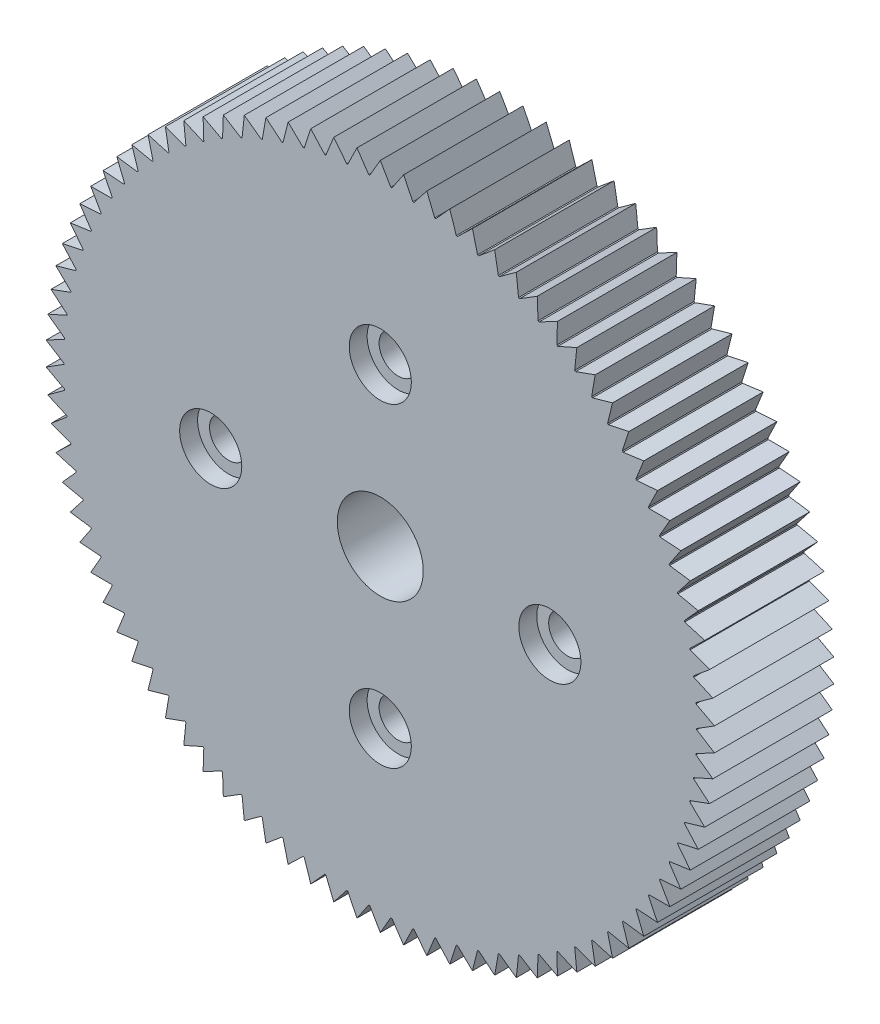
SolidWorks part; units mm, degrees
ref_plane "Front Plane" through (0, 0, 0) normal (0, 0, 1) x (1, 0, 0)
ref_plane "Top Plane" through (0, 0, 0) normal (0, 1, 0) x (1, 0, 0)
ref_plane "Right Plane" through (0, 0, 0) normal (1, 0, 0) x (0, 0, -1)
sketch "Sketch1" plane through (0, 0, 0) normal (0, 0, 1) x (1, 0, 0)
  circle A0 centre (0, 0) radius 13.25
  dimension "D1" = 26.5
extrude "Extrude1" add sketch "Sketch1" along normal blind 5
sketch "Sketch2" plane through (0, 0, 0) normal (0, 0, -1) x (-1, 0, 0)
  line L0 (-7.1, 1.675) -> (-2.3674, 1.675)
  line L1 (1.675, 6.6) -> (1.675, 2.3674)
  line L2 (-7.1, -1.675) -> (-2.3674, -1.675)
  line L3 (-1.675, 6.6) -> (-1.675, 2.3674)
  line L4 (-1.675, -2.3674) -> (-1.675, -6.6)
  line L5 (1.675, -2.3674) -> (1.675, -6.6)
  line L6 (2.3674, -1.675) -> (7.1, -1.675)
  line L7 (2.3674, 1.675) -> (7.1, 1.675)
  circle A0 centre (0, -6.6) radius 1.675 construction
  circle A1 centre (0, 6.6) radius 1.675 construction
  circle A2 centre (-7.1, 0) radius 1.675 construction
  circle A3 centre (7.1, 0) radius 1.675 construction
  arc A4 (-2.3674, -1.675) -> (-1.675, -2.3674) centre (0, 0) ccw
  arc A5 (-7.1, 1.675) -> (-7.1, -1.675) centre (-7.1, 0) ccw
  arc A6 (-1.675, -6.6) -> (1.675, -6.6) centre (0, -6.6) ccw
  arc A7 (7.1, 1.675) -> (7.1, -1.675) centre (7.1, 0) cw
  arc A8 (-1.675, 6.6) -> (1.675, 6.6) centre (0, 6.6) cw
  circle A9 centre (0, 0) radius 2.9 construction
  arc A10 (-2.3674, 1.675) -> (-1.675, 2.3674) centre (0, 0) cw
  arc A11 (1.675, 2.3674) -> (2.3674, 1.675) centre (0, 0) cw
  arc A12 (2.3674, -1.675) -> (1.675, -2.3674) centre (0, 0) cw
  dimension "D1" = 4.7326
extrude "Extrude2" cut sketch "Sketch2" against normal blind 1.2
sketch "Sketch3" plane through (0, 0, 1.2) normal (0, 0, -1) x (-1, 0, 0)
  circle A0 centre (0, 0) radius 1.8
extrude "Extrude3" cut sketch "Sketch3" against normal through all
sketch "Sketch4" plane through (0, 0, 1.2) normal (0, 0, -1) x (-1, 0, 0)
  circle A0 centre (0, 6.6) radius 0.8
  circle A1 centre (-7.1, 0) radius 0.8
  circle A2 centre (0, -6.6) radius 0.8
  circle A3 centre (7.1, 0) radius 0.8
extrude "Extrude4" cut sketch "Sketch4" against normal through all
sketch "Sketch5" plane through (0, 0, 5) normal (0, 0, 1) x (1, 0, 0)
  circle A0 centre (-7.1, 0) radius 1.3
  circle A1 centre (0, -6.6) radius 1.3
  circle A2 centre (7.1, 0) radius 1.3
  circle A3 centre (0, 6.6) radius 1.3
extrude "Extrude5" cut sketch "Sketch5" against normal blind 0.75
sketch "Sketch6" plane through (0, 0, 0) normal (0, 0, -1) x (-1, 0, 0)
  line L0 (0, 13.25) -> (0, 14) construction
  line L1 (0, 14) -> (-0.4393, 13.2427)
  line L2 (0.4393, 13.2427) -> (0, 14)
  line L181 (1.362, 13.1798) -> (0.9766, 13.9659)
  line L182 (0.9766, 13.9659) -> (0.4855, 13.2411)
  line L183 (2.2781, 13.0527) -> (1.9484, 13.8638)
  line L184 (1.9484, 13.8638) -> (1.408, 13.175)
  line L185 (3.183, 12.862) -> (2.9108, 13.6941)
  line L186 (2.9108, 13.6941) -> (2.3236, 13.0447)
  line L187 (4.0725, 12.6086) -> (3.8589, 13.4577)
  line L188 (3.8589, 13.4577) -> (3.2279, 12.8508)
  line L189 (4.9421, 12.2938) -> (4.7883, 13.1557)
  line L190 (4.7883, 13.1557) -> (4.1165, 12.5943)
  line L191 (5.7876, 11.9191) -> (5.6943, 12.7896)
  line L192 (5.6943, 12.7896) -> (4.985, 12.2765)
  line L193 (6.605, 11.4864) -> (6.5726, 12.3613)
  line L194 (6.5726, 12.3613) -> (5.8292, 11.8989)
  line L195 (7.3901, 10.9977) -> (7.4189, 11.8727)
  line L196 (7.4189, 11.8727) -> (6.645, 11.4633)
  line L197 (8.1393, 10.4554) -> (8.229, 11.3262)
  line L198 (8.229, 11.3262) -> (7.4285, 10.9718)
  line L199 (8.8488, 9.8621) -> (8.999, 10.7246)
  line L200 (8.999, 10.7246) -> (8.1757, 10.4269)
  line L201 (9.5152, 9.2208) -> (9.7252, 10.0708)
  line L202 (9.7252, 10.0708) -> (8.8832, 9.8312)
  line L203 (10.1352, 8.5346) -> (10.404, 9.3678)
  line L204 (10.404, 9.3678) -> (9.5473, 9.1876)
  line L205 (10.7059, 7.8069) -> (11.0322, 8.6193)
  line L206 (11.0322, 8.6193) -> (10.1649, 8.4992)
  line L207 (11.2244, 7.041) -> (11.6065, 7.8287)
  line L208 (11.6065, 7.8287) -> (10.7331, 7.7694)
  line L209 (11.6882, 6.2409) -> (12.1244, 7)
  line L210 (12.1244, 7) -> (11.2489, 7.0018)
  line L211 (12.0951, 5.4104) -> (12.5831, 6.1372)
  line L212 (12.5831, 6.1372) -> (11.7099, 6.2001)
  line L213 (12.443, 4.5535) -> (12.9806, 5.2445)
  line L214 (12.9806, 5.2445) -> (12.1139, 5.3681)
  line L215 (12.7303, 3.6744) -> (13.3148, 4.3262)
  line L216 (13.3148, 4.3262) -> (12.4588, 4.51)
  line L217 (12.9556, 2.7774) -> (13.5841, 3.3869)
  line L218 (13.5841, 3.3869) -> (12.7431, 3.63)
  line L219 (13.1178, 1.8669) -> (13.7873, 2.4311)
  line L220 (13.7873, 2.4311) -> (12.9652, 2.7322)
  line L221 (13.2161, 0.9473) -> (13.9233, 1.4634)
  line L222 (13.9233, 1.4634) -> (13.1243, 1.8211)
  line L223 (13.25, 0.0231) -> (13.9915, 0.4886)
  line L224 (13.9915, 0.4886) -> (13.2193, 0.9012)
  line L225 (13.2193, -0.9012) -> (13.9915, -0.4886)
  line L226 (13.9915, -0.4886) -> (13.25, -0.0231)
  line L227 (13.1243, -1.8211) -> (13.9233, -1.4634)
  line L228 (13.9233, -1.4634) -> (13.2161, -0.9473)
  line L229 (12.9652, -2.7322) -> (13.7873, -2.4311)
  line L230 (13.7873, -2.4311) -> (13.1178, -1.8669)
  line L231 (12.7431, -3.63) -> (13.5841, -3.3869)
  line L232 (13.5841, -3.3869) -> (12.9556, -2.7774)
  line L233 (12.4588, -4.51) -> (13.3148, -4.3262)
  line L234 (13.3148, -4.3262) -> (12.7303, -3.6744)
  line L235 (12.1139, -5.3681) -> (12.9806, -5.2445)
  line L236 (12.9806, -5.2445) -> (12.443, -4.5535)
  line L237 (11.7099, -6.2001) -> (12.5831, -6.1372)
  line L238 (12.5831, -6.1372) -> (12.0951, -5.4104)
  line L239 (11.2489, -7.0018) -> (12.1244, -7)
  line L240 (12.1244, -7) -> (11.6882, -6.2409)
  line L241 (10.7331, -7.7694) -> (11.6065, -7.8287)
  line L242 (11.6065, -7.8287) -> (11.2244, -7.041)
  line L243 (10.1649, -8.4992) -> (11.0322, -8.6193)
  line L244 (11.0322, -8.6193) -> (10.7059, -7.8069)
  line L245 (9.5473, -9.1876) -> (10.404, -9.3678)
  line L246 (10.404, -9.3678) -> (10.1352, -8.5346)
  line L247 (8.8832, -9.8312) -> (9.7252, -10.0708)
  line L248 (9.7252, -10.0708) -> (9.5152, -9.2208)
  line L249 (8.1757, -10.4269) -> (8.999, -10.7246)
  line L250 (8.999, -10.7246) -> (8.8488, -9.8621)
  line L251 (7.4285, -10.9718) -> (8.229, -11.3262)
  line L252 (8.229, -11.3262) -> (8.1393, -10.4554)
  line L253 (6.645, -11.4633) -> (7.4189, -11.8727)
  line L254 (7.4189, -11.8727) -> (7.3901, -10.9977)
  line L255 (5.8292, -11.8989) -> (6.5726, -12.3613)
  line L256 (6.5726, -12.3613) -> (6.605, -11.4864)
  line L257 (4.985, -12.2765) -> (5.6943, -12.7896)
  line L258 (5.6943, -12.7896) -> (5.7876, -11.9191)
  line L259 (4.1165, -12.5943) -> (4.7883, -13.1557)
  line L260 (4.7883, -13.1557) -> (4.9421, -12.2938)
  line L261 (3.2279, -12.8508) -> (3.8589, -13.4577)
  line L262 (3.8589, -13.4577) -> (4.0725, -12.6086)
  line L263 (2.3236, -13.0447) -> (2.9108, -13.6941)
  line L264 (2.9108, -13.6941) -> (3.183, -12.862)
  line L265 (1.408, -13.175) -> (1.9484, -13.8638)
  line L266 (1.9484, -13.8638) -> (2.2781, -13.0527)
  line L267 (0.4855, -13.2411) -> (0.9766, -13.9659)
  line L268 (0.9766, -13.9659) -> (1.362, -13.1798)
  line L269 (-0.4393, -13.2427) -> (0, -14)
  line L270 (0, -14) -> (0.4393, -13.2427)
  line L271 (-1.362, -13.1798) -> (-0.9766, -13.9659)
  line L272 (-0.9766, -13.9659) -> (-0.4855, -13.2411)
  line L273 (-2.2781, -13.0527) -> (-1.9484, -13.8638)
  line L274 (-1.9484, -13.8638) -> (-1.408, -13.175)
  line L275 (-3.183, -12.862) -> (-2.9108, -13.6941)
  line L276 (-2.9108, -13.6941) -> (-2.3236, -13.0447)
  line L277 (-4.0725, -12.6086) -> (-3.8589, -13.4577)
  line L278 (-3.8589, -13.4577) -> (-3.2279, -12.8508)
  line L279 (-4.9421, -12.2938) -> (-4.7883, -13.1557)
  line L280 (-4.7883, -13.1557) -> (-4.1165, -12.5943)
  line L281 (-5.7876, -11.9191) -> (-5.6943, -12.7896)
  line L282 (-5.6943, -12.7896) -> (-4.985, -12.2765)
  line L283 (-6.605, -11.4864) -> (-6.5726, -12.3613)
  line L284 (-6.5726, -12.3613) -> (-5.8292, -11.8989)
  line L285 (-7.3901, -10.9977) -> (-7.4189, -11.8727)
  line L286 (-7.4189, -11.8727) -> (-6.645, -11.4633)
  line L287 (-8.1393, -10.4554) -> (-8.229, -11.3262)
  line L288 (-8.229, -11.3262) -> (-7.4285, -10.9718)
  line L289 (-8.8488, -9.8621) -> (-8.999, -10.7246)
  line L290 (-8.999, -10.7246) -> (-8.1757, -10.4269)
  line L291 (-9.5152, -9.2208) -> (-9.7252, -10.0708)
  line L292 (-9.7252, -10.0708) -> (-8.8832, -9.8312)
  line L293 (-10.1352, -8.5346) -> (-10.404, -9.3678)
  line L294 (-10.404, -9.3678) -> (-9.5473, -9.1876)
  line L295 (-10.7059, -7.8069) -> (-11.0322, -8.6193)
  line L296 (-11.0322, -8.6193) -> (-10.1649, -8.4992)
  line L297 (-11.2244, -7.041) -> (-11.6065, -7.8287)
  line L298 (-11.6065, -7.8287) -> (-10.7331, -7.7694)
  line L299 (-11.6882, -6.2409) -> (-12.1244, -7)
  line L300 (-12.1244, -7) -> (-11.2489, -7.0018)
  line L301 (-12.0951, -5.4104) -> (-12.5831, -6.1372)
  line L302 (-12.5831, -6.1372) -> (-11.7099, -6.2001)
  line L303 (-12.443, -4.5535) -> (-12.9806, -5.2445)
  line L304 (-12.9806, -5.2445) -> (-12.1139, -5.3681)
  line L305 (-12.7303, -3.6744) -> (-13.3148, -4.3262)
  line L306 (-13.3148, -4.3262) -> (-12.4588, -4.51)
  line L307 (-12.9556, -2.7774) -> (-13.5841, -3.3869)
  line L308 (-13.5841, -3.3869) -> (-12.7431, -3.63)
  line L309 (-13.1178, -1.8669) -> (-13.7873, -2.4311)
  line L310 (-13.7873, -2.4311) -> (-12.9652, -2.7322)
  line L311 (-13.2161, -0.9473) -> (-13.9233, -1.4634)
  line L312 (-13.9233, -1.4634) -> (-13.1243, -1.8211)
  line L313 (-13.25, -0.0231) -> (-13.9915, -0.4886)
  line L314 (-13.9915, -0.4886) -> (-13.2193, -0.9012)
  line L315 (-13.2193, 0.9012) -> (-13.9915, 0.4886)
  line L316 (-13.9915, 0.4886) -> (-13.25, 0.0231)
  line L317 (-13.1243, 1.8211) -> (-13.9233, 1.4634)
  line L318 (-13.9233, 1.4634) -> (-13.2161, 0.9473)
  line L319 (-12.9652, 2.7322) -> (-13.7873, 2.4311)
  line L320 (-13.7873, 2.4311) -> (-13.1178, 1.8669)
  line L321 (-12.7431, 3.63) -> (-13.5841, 3.3869)
  line L322 (-13.5841, 3.3869) -> (-12.9556, 2.7774)
  line L323 (-12.4588, 4.51) -> (-13.3148, 4.3262)
  line L324 (-13.3148, 4.3262) -> (-12.7303, 3.6744)
  line L325 (-12.1139, 5.3681) -> (-12.9806, 5.2445)
  line L326 (-12.9806, 5.2445) -> (-12.443, 4.5535)
  line L327 (-11.7099, 6.2001) -> (-12.5831, 6.1372)
  line L328 (-12.5831, 6.1372) -> (-12.0951, 5.4104)
  line L329 (-11.2489, 7.0018) -> (-12.1244, 7)
  line L330 (-12.1244, 7) -> (-11.6882, 6.2409)
  line L331 (-10.7331, 7.7694) -> (-11.6065, 7.8287)
  line L332 (-11.6065, 7.8287) -> (-11.2244, 7.041)
  line L333 (-10.1649, 8.4992) -> (-11.0322, 8.6193)
  line L334 (-11.0322, 8.6193) -> (-10.7059, 7.8069)
  line L335 (-9.5473, 9.1876) -> (-10.404, 9.3678)
  line L336 (-10.404, 9.3678) -> (-10.1352, 8.5346)
  line L337 (-8.8832, 9.8312) -> (-9.7252, 10.0708)
  line L338 (-9.7252, 10.0708) -> (-9.5152, 9.2208)
  line L339 (-8.1757, 10.4269) -> (-8.999, 10.7246)
  line L340 (-8.999, 10.7246) -> (-8.8488, 9.8621)
  line L341 (-7.4285, 10.9718) -> (-8.229, 11.3262)
  line L342 (-8.229, 11.3262) -> (-8.1393, 10.4554)
  line L343 (-6.645, 11.4633) -> (-7.4189, 11.8727)
  line L344 (-7.4189, 11.8727) -> (-7.3901, 10.9977)
  line L345 (-5.8292, 11.8989) -> (-6.5726, 12.3613)
  line L346 (-6.5726, 12.3613) -> (-6.605, 11.4864)
  line L347 (-4.985, 12.2765) -> (-5.6943, 12.7896)
  line L348 (-5.6943, 12.7896) -> (-5.7876, 11.9191)
  line L349 (-4.1165, 12.5943) -> (-4.7883, 13.1557)
  line L350 (-4.7883, 13.1557) -> (-4.9421, 12.2938)
  line L351 (-3.2279, 12.8508) -> (-3.8589, 13.4577)
  line L352 (-3.8589, 13.4577) -> (-4.0725, 12.6086)
  line L353 (-2.3236, 13.0447) -> (-2.9108, 13.6941)
  line L354 (-2.9108, 13.6941) -> (-3.183, 12.862)
  line L355 (-1.408, 13.175) -> (-1.9484, 13.8638)
  line L356 (-1.9484, 13.8638) -> (-2.2781, 13.0527)
  line L357 (-0.4855, 13.2411) -> (-0.9766, 13.9659)
  line L358 (-0.9766, 13.9659) -> (-1.362, 13.1798)
  circle A0 centre (0, 0) radius 13.25 construction
  arc A1 (-0.4393, 13.2427) -> (0.4393, 13.2427) centre (0, 0) cw
  arc A91 (0.4855, 13.2411) -> (1.362, 13.1798) centre (0, 0) cw
  arc A92 (1.408, 13.175) -> (2.2781, 13.0527) centre (0, 0) cw
  arc A93 (2.3236, 13.0447) -> (3.183, 12.862) centre (0, 0) cw
  arc A94 (3.2279, 12.8508) -> (4.0725, 12.6086) centre (0, 0) cw
  arc A95 (4.1165, 12.5943) -> (4.9421, 12.2938) centre (0, 0) cw
  arc A96 (4.985, 12.2765) -> (5.7876, 11.9191) centre (0, 0) cw
  arc A97 (5.8292, 11.8989) -> (6.605, 11.4864) centre (0, 0) cw
  arc A98 (6.645, 11.4633) -> (7.3901, 10.9977) centre (0, 0) cw
  arc A99 (7.4285, 10.9718) -> (8.1393, 10.4554) centre (0, 0) cw
  arc A100 (8.1757, 10.4269) -> (8.8488, 9.8621) centre (0, 0) cw
  arc A101 (8.8832, 9.8312) -> (9.5152, 9.2208) centre (0, 0) cw
  arc A102 (9.5473, 9.1876) -> (10.1352, 8.5346) centre (0, 0) cw
  arc A103 (10.1649, 8.4992) -> (10.7059, 7.8069) centre (0, 0) cw
  arc A104 (10.7331, 7.7694) -> (11.2244, 7.041) centre (0, 0) cw
  arc A105 (11.2489, 7.0018) -> (11.6882, 6.2409) centre (0, 0) cw
  arc A106 (11.7099, 6.2001) -> (12.0951, 5.4104) centre (0, 0) cw
  arc A107 (12.1139, 5.3681) -> (12.443, 4.5535) centre (0, 0) cw
  arc A108 (12.4588, 4.51) -> (12.7303, 3.6744) centre (0, 0) cw
  arc A109 (12.7431, 3.63) -> (12.9556, 2.7774) centre (0, 0) cw
  arc A110 (12.9652, 2.7322) -> (13.1178, 1.8669) centre (0, 0) cw
  arc A111 (13.1243, 1.8211) -> (13.2161, 0.9473) centre (0, 0) cw
  arc A112 (13.2193, 0.9012) -> (13.25, 0.0231) centre (0, 0) cw
  arc A113 (13.25, -0.0231) -> (13.2193, -0.9012) centre (0, 0) cw
  arc A114 (13.2161, -0.9473) -> (13.1243, -1.8211) centre (0, 0) cw
  arc A115 (13.1178, -1.8669) -> (12.9652, -2.7322) centre (0, 0) cw
  arc A116 (12.9556, -2.7774) -> (12.7431, -3.63) centre (0, 0) cw
  arc A117 (12.7303, -3.6744) -> (12.4588, -4.51) centre (0, 0) cw
  arc A118 (12.443, -4.5535) -> (12.1139, -5.3681) centre (0, 0) cw
  arc A119 (12.0951, -5.4104) -> (11.7099, -6.2001) centre (0, 0) cw
  arc A120 (11.6882, -6.2409) -> (11.2489, -7.0018) centre (0, 0) cw
  arc A121 (11.2244, -7.041) -> (10.7331, -7.7694) centre (0, 0) cw
  arc A122 (10.7059, -7.8069) -> (10.1649, -8.4992) centre (0, 0) cw
  arc A123 (10.1352, -8.5346) -> (9.5473, -9.1876) centre (0, 0) cw
  arc A124 (9.5152, -9.2208) -> (8.8832, -9.8312) centre (0, 0) cw
  arc A125 (8.8488, -9.8621) -> (8.1757, -10.4269) centre (0, 0) cw
  arc A126 (8.1393, -10.4554) -> (7.4285, -10.9718) centre (0, 0) cw
  arc A127 (7.3901, -10.9977) -> (6.645, -11.4633) centre (0, 0) cw
  arc A128 (6.605, -11.4864) -> (5.8292, -11.8989) centre (0, 0) cw
  arc A129 (5.7876, -11.9191) -> (4.985, -12.2765) centre (0, 0) cw
  arc A130 (4.9421, -12.2938) -> (4.1165, -12.5943) centre (0, 0) cw
  arc A131 (4.0725, -12.6086) -> (3.2279, -12.8508) centre (0, 0) cw
  arc A132 (3.183, -12.862) -> (2.3236, -13.0447) centre (0, 0) cw
  arc A133 (2.2781, -13.0527) -> (1.408, -13.175) centre (0, 0) cw
  arc A134 (1.362, -13.1798) -> (0.4855, -13.2411) centre (0, 0) cw
  arc A135 (0.4393, -13.2427) -> (-0.4393, -13.2427) centre (0, 0) cw
  arc A136 (-0.4855, -13.2411) -> (-1.362, -13.1798) centre (0, 0) cw
  arc A137 (-1.408, -13.175) -> (-2.2781, -13.0527) centre (0, 0) cw
  arc A138 (-2.3236, -13.0447) -> (-3.183, -12.862) centre (0, 0) cw
  arc A139 (-3.2279, -12.8508) -> (-4.0725, -12.6086) centre (0, 0) cw
  arc A140 (-4.1165, -12.5943) -> (-4.9421, -12.2938) centre (0, 0) cw
  arc A141 (-4.985, -12.2765) -> (-5.7876, -11.9191) centre (0, 0) cw
  arc A142 (-5.8292, -11.8989) -> (-6.605, -11.4864) centre (0, 0) cw
  arc A143 (-6.645, -11.4633) -> (-7.3901, -10.9977) centre (0, 0) cw
  arc A144 (-7.4285, -10.9718) -> (-8.1393, -10.4554) centre (0, 0) cw
  arc A145 (-8.1757, -10.4269) -> (-8.8488, -9.8621) centre (0, 0) cw
  arc A146 (-8.8832, -9.8312) -> (-9.5152, -9.2208) centre (0, 0) cw
  arc A147 (-9.5473, -9.1876) -> (-10.1352, -8.5346) centre (0, 0) cw
  arc A148 (-10.1649, -8.4992) -> (-10.7059, -7.8069) centre (0, 0) cw
  arc A149 (-10.7331, -7.7694) -> (-11.2244, -7.041) centre (0, 0) cw
  arc A150 (-11.2489, -7.0018) -> (-11.6882, -6.2409) centre (0, 0) cw
  arc A151 (-11.7099, -6.2001) -> (-12.0951, -5.4104) centre (0, 0) cw
  arc A152 (-12.1139, -5.3681) -> (-12.443, -4.5535) centre (0, 0) cw
  arc A153 (-12.4588, -4.51) -> (-12.7303, -3.6744) centre (0, 0) cw
  arc A154 (-12.7431, -3.63) -> (-12.9556, -2.7774) centre (0, 0) cw
  arc A155 (-12.9652, -2.7322) -> (-13.1178, -1.8669) centre (0, 0) cw
  arc A156 (-13.1243, -1.8211) -> (-13.2161, -0.9473) centre (0, 0) cw
  arc A157 (-13.2193, -0.9012) -> (-13.25, -0.0231) centre (0, 0) cw
  arc A158 (-13.25, 0.0231) -> (-13.2193, 0.9012) centre (0, 0) cw
  arc A159 (-13.2161, 0.9473) -> (-13.1243, 1.8211) centre (0, 0) cw
  arc A160 (-13.1178, 1.8669) -> (-12.9652, 2.7322) centre (0, 0) cw
  arc A161 (-12.9556, 2.7774) -> (-12.7431, 3.63) centre (0, 0) cw
  arc A162 (-12.7303, 3.6744) -> (-12.4588, 4.51) centre (0, 0) cw
  arc A163 (-12.443, 4.5535) -> (-12.1139, 5.3681) centre (0, 0) cw
  arc A164 (-12.0951, 5.4104) -> (-11.7099, 6.2001) centre (0, 0) cw
  arc A165 (-11.6882, 6.2409) -> (-11.2489, 7.0018) centre (0, 0) cw
  arc A166 (-11.2244, 7.041) -> (-10.7331, 7.7694) centre (0, 0) cw
  arc A167 (-10.7059, 7.8069) -> (-10.1649, 8.4992) centre (0, 0) cw
  arc A168 (-10.1352, 8.5346) -> (-9.5473, 9.1876) centre (0, 0) cw
  arc A169 (-9.5152, 9.2208) -> (-8.8832, 9.8312) centre (0, 0) cw
  arc A170 (-8.8488, 9.8621) -> (-8.1757, 10.4269) centre (0, 0) cw
  arc A171 (-8.1393, 10.4554) -> (-7.4285, 10.9718) centre (0, 0) cw
  arc A172 (-7.3901, 10.9977) -> (-6.645, 11.4633) centre (0, 0) cw
  arc A173 (-6.605, 11.4864) -> (-5.8292, 11.8989) centre (0, 0) cw
  arc A174 (-5.7876, 11.9191) -> (-4.985, 12.2765) centre (0, 0) cw
  arc A175 (-4.9421, 12.2938) -> (-4.1165, 12.5943) centre (0, 0) cw
  arc A176 (-4.0725, 12.6086) -> (-3.2279, 12.8508) centre (0, 0) cw
  arc A177 (-3.183, 12.862) -> (-2.3236, 13.0447) centre (0, 0) cw
  arc A178 (-2.2781, 13.0527) -> (-1.408, 13.175) centre (0, 0) cw
  arc A179 (-1.362, 13.1798) -> (-0.4855, 13.2411) centre (0, 0) cw
  point P9 (0, 13.25)
  dimension "D1" = 0.75
extrude "Extrude6" add sketch "Sketch6" against normal up to surface (5 mm away) up to face at (1.3, 6.6, 5)
